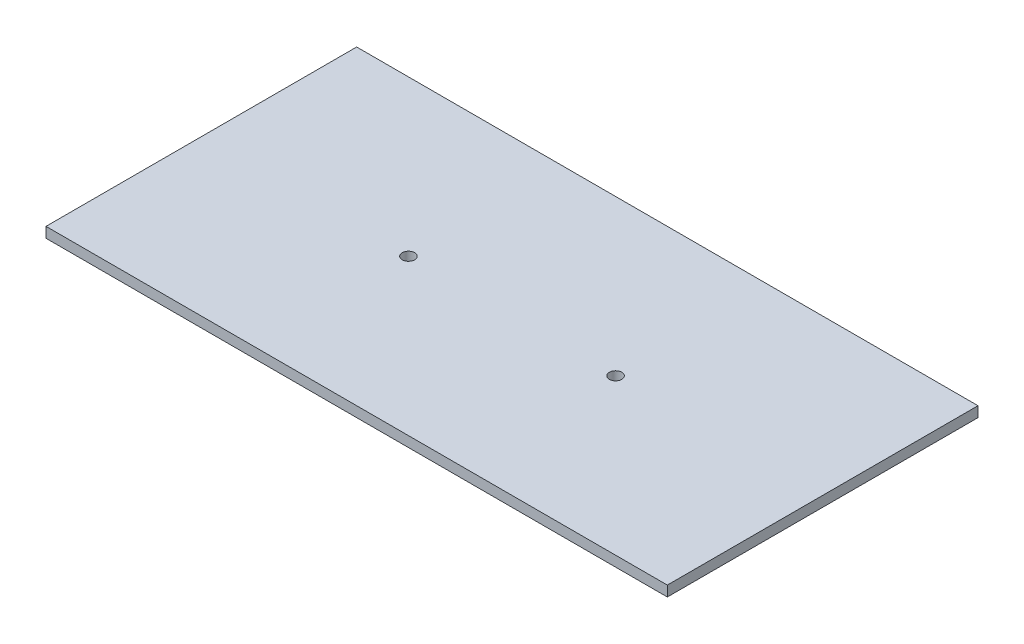
SolidWorks part; units mm, degrees
ref_plane "Front Plane" through (0, 0, 0) normal (0, 0, 1) x (1, 0, 0)
ref_plane "Top Plane" through (0, 0, 0) normal (0, 1, 0) x (1, 0, 0)
ref_plane "Right Plane" through (0, 0, 0) normal (1, 0, 0) x (0, 0, -1)
sketch "Sketch1" plane through (0, 0, 0) normal (0, 1, 0) x (1, 0, 0)
  line L1 (-150, -75) -> (150, -75)
  line L2 (-150, -75) -> (-150, 75)
  line L3 (-150, 75) -> (150, 75)
  line L4 (150, -75) -> (150, 75)
  line L5 (-150, -75) -> (150, 75) construction
  line L6 (-150, 75) -> (150, -75) construction
  point P0 (0, 0)
  dimension "D1" = 300
  dimension "D2" = 150
extrude "Boss-Extrude1" add sketch "Sketch1" along normal blind 5
sketch "Sketch2" plane through (0, 5, 0) normal (0, 1, 0) x (1, 0, 0)
  line L0 (-150, 75) -> (-150, -75) construction
  line L1 (0, -2.75) -> (0, 2.75) construction
  circle A0 centre (-50, 0) radius 3
  circle A1 centre (50, 0) radius 3
  point P2 (0, 0)
  point P5 (0, 0)
  dimension "D1" = 6
  dimension "D2" = 100
extrude "Cut-Extrude1" cut sketch "Sketch2" against normal up to next
